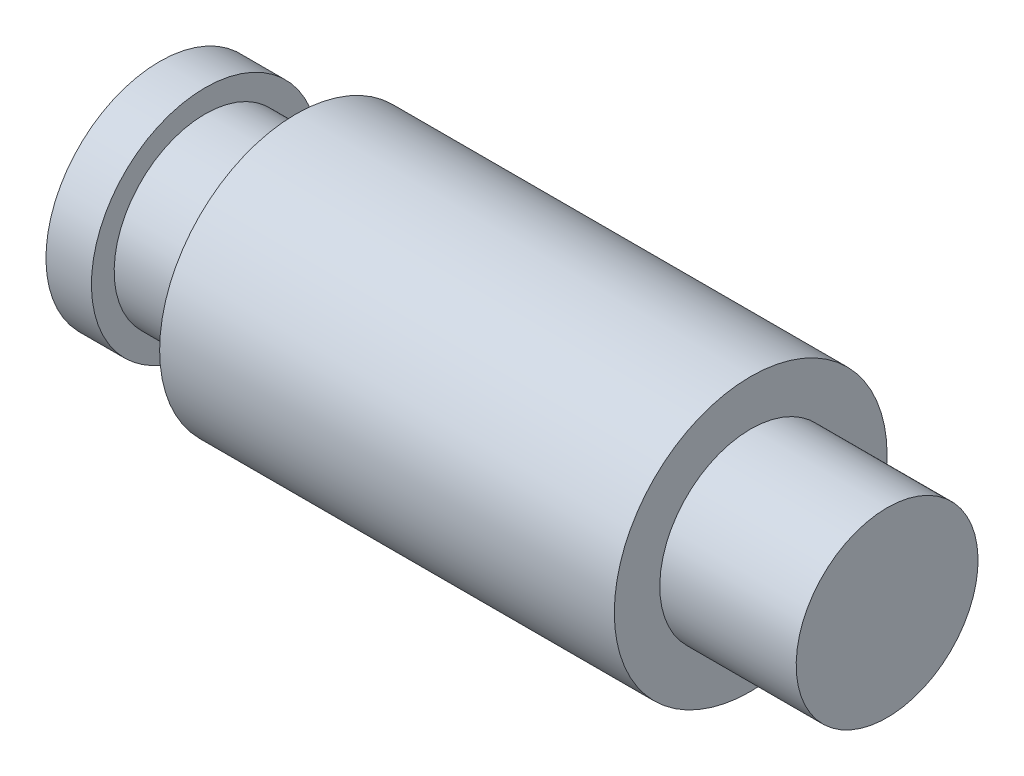
SolidWorks part; units mm, degrees
ref_plane "Face" through (0, 0, 0) normal (0, 0, 1) x (1, 0, 0)
ref_plane "Dessus" through (0, 0, 0) normal (0, 1, 0) x (1, 0, 0)
ref_plane "Droite" through (0, 0, 0) normal (1, 0, 0) x (0, 0, -1)
sketch "Esquisse1" plane through (0, 0, 0) normal (0, 0, 1) x (1, 0, 0)
  line L0 (0, 0) -> (0, 2.5)
  line L1 (0, 2.5) -> (1, 2.5)
  line L2 (1, 2.5) -> (1, 2)
  line L3 (3, 2) -> (3, 3)
  line L4 (3, 3) -> (13, 3)
  line L5 (16, 2) -> (16, 0)
  line L6 (16, 0) -> (0, 0)
  line L7 (1, 2) -> (3, 2)
  line L8 (13, 3) -> (13, 2)
  line L9 (13, 2) -> (16, 2)
  dimension "D1" = 2.5
  dimension "D2" = 1
  dimension "D3" = 2
  dimension "D4" = 2
  dimension "D5" = 3
  dimension "D6" = 16
  dimension "D7" = 2
  dimension "D8" = 3
revolve "Révolution1" add sketch "Esquisse1" angle 360 about L6
